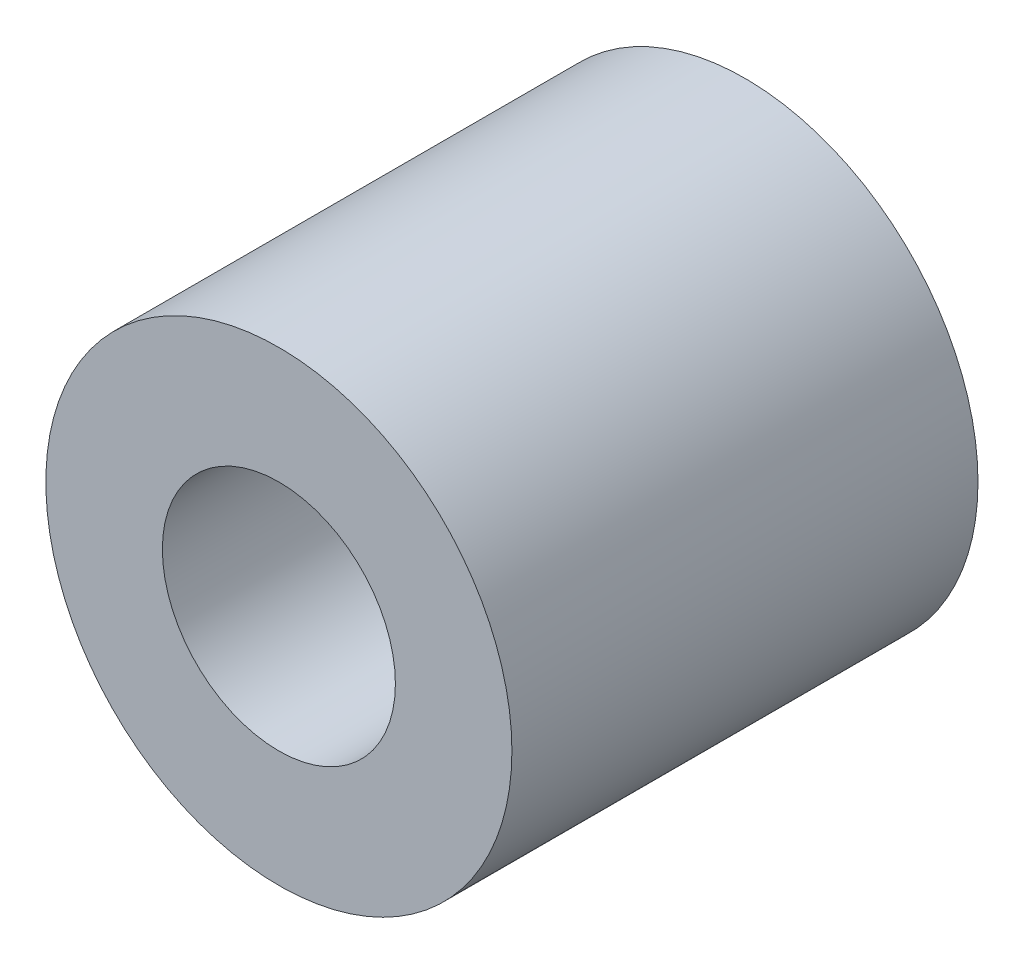
SolidWorks part; units mm, degrees
ref_plane "前视基准面" through (0, 0, 0) normal (0, 0, 1) x (1, 0, 0)
ref_plane "上视基准面" through (0, 0, 0) normal (0, 1, 0) x (1, 0, 0)
ref_plane "右视基准面" through (0, 0, 0) normal (1, 0, 0) x (0, 0, -1)
sketch "草图1" plane through (0, 0, 0) normal (0, 0, 1) x (1, 0, 0)
  circle A0 centre (0, 0) radius 8
  circle A1 centre (0, 0) radius 4
  dimension "D1" = 16
extrude "凸台-拉伸1" add sketch "草图1" along normal blind 16
